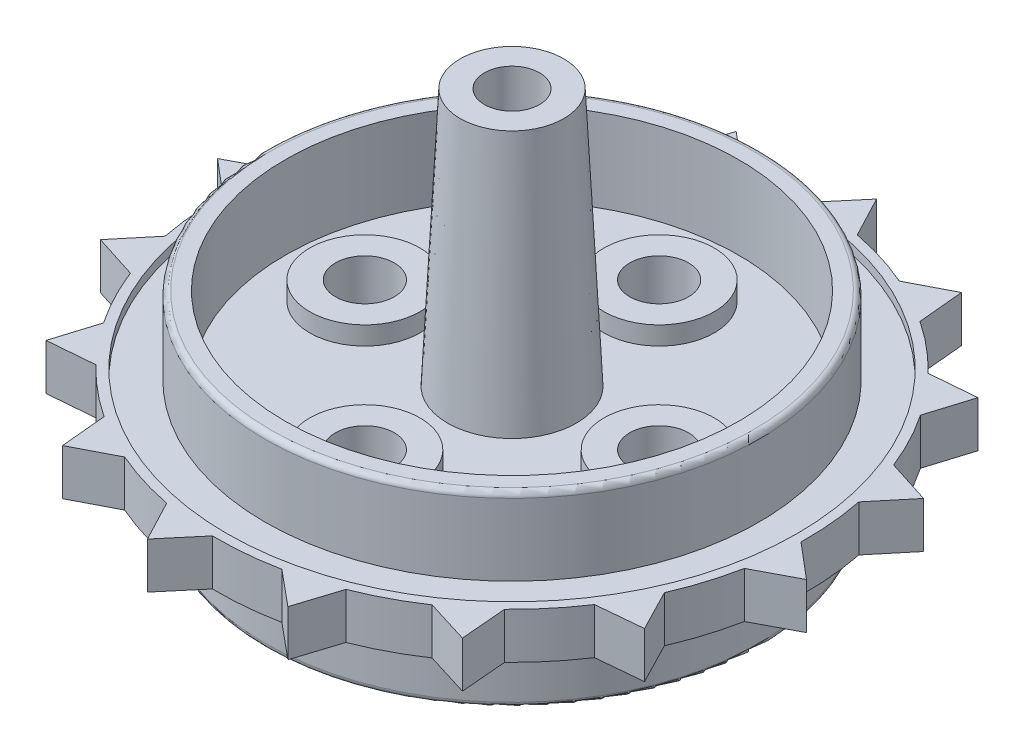
SolidWorks part; units mm, degrees
ref_plane "Front Plane" through (0, 0, 0) normal (0, 0, 1) x (1, 0, 0)
ref_plane "Top Plane" through (0, 0, 0) normal (0, 1, 0) x (1, 0, 0)
ref_plane "Right Plane" through (0, 0, 0) normal (1, 0, 0) x (0, 0, -1)
sketch "Sketch1" plane through (0, 0, 0) normal (0, 1, 0) x (1, 0, 0)
  circle A0 centre (0, 0) radius 13.425
  dimension "D1" = 26.85
extrude "Boss-Extrude1" add sketch "Sketch1" along normal blind 4
sketch "Sketch2" plane through (0, 4, 0) normal (0, 1, 0) x (1, 0, 0)
  circle A0 centre (0, 0) radius 16
  dimension "D1" = 32
extrude "Boss-Extrude2" add sketch "Sketch2" along normal blind 2.5
sketch "Sketch4" plane through (0, 0, 0) normal (0, -1, 0) x (1, 0, 0)
  circle A0 centre (0, 0) radius 12.325
  circle A1 centre (0, 0) radius 13.425 construction
  dimension "D1" = 1.1
extrude "Cut-Extrude1" cut sketch "Sketch4" against normal blind 4
sketch "Sketch5" plane through (0, 4, 0) normal (0, -1, 0) x (1, 0, 0)
  circle A0 centre (0, 0) radius 15.5
  circle A1 centre (0, 0) radius 16 construction
  dimension "D1" = 0.5
sketch "Sketch6" plane through (0, 6.5, 0) normal (0, 1, 0) x (1, 0, 0)
  circle A0 centre (0, 0) radius 15.5
  circle A1 centre (0, 0) radius 16 construction
  dimension "D1" = 0.5
extrude "Cut-Extrude3" cut sketch "Sketch6" against normal blind 0.5
extrude "Cut-Extrude4" cut sketch "Sketch5" against normal blind 0.5
sketch "Sketch7" plane through (0, 4.5, 0) normal (0, -1, 0) x (1, 0, 0)
  circle A0 centre (0, 0) radius 5.5
  circle A1 centre (0, 8) radius 3
  circle A2 centre (8, 0) radius 3
  circle A3 centre (0, -8) radius 3
  circle A4 centre (-8, 0) radius 3
  point P14 (0, 0)
  dimension "D1" = 11
  dimension "D2" = 6
  dimension "D3" = 8
  dimension "D4" = 0
  dimension "D6" = 11.3137
  dimension "D5" = 4
extrude "Boss-Extrude4" add sketch "Sketch7" along normal blind 1 contours A0 | A1 | A4 | A3 | A2
sketch "Sketch8" plane through (0, 3.5, 0) normal (0, -1, 0) x (1, 0, 0)
  circle A0 centre (0, 0) radius 3.2
  dimension "D1" = 6.4
extrude "Boss-Extrude5" add sketch "Sketch8" along normal blind 4.3
fillet "Fillet1" radius 1 1 edges at (0, -0.8, -3.2)
sketch "Sketch10" plane through (0, 6, 0) normal (0, 1, 0) x (1, 0, 0)
  circle A0 centre (0, 0) radius 13.425
  dimension "D1" = 26.85
extrude "Boss-Extrude6" add sketch "Sketch10" along normal blind 4.2
sketch "Sketch11" plane through (0, 10.2, 0) normal (0, 1, 0) x (1, 0, 0)
  circle A0 centre (0, 0) radius 12.325
  circle A1 centre (0, 0) radius 13.425 construction
  dimension "D1" = 1.1
extrude "Cut-Extrude6" cut sketch "Sketch11" against normal blind 4.5
sketch "Sketch12" plane through (0, 5.7, 0) normal (0, 1, 0) x (1, 0, 0)
  circle A0 centre (0, 0) radius 3.5
  dimension "D1" = 7
extrude "Boss-Extrude7" add sketch "Sketch12" along normal blind 14 draft 2.8
sketch "Sketch13" plane through (0, 19.7, 0) normal (0, 1, 0) x (1, 0, 0)
  circle A0 centre (0, 0) radius 1.5
  dimension "D1" = 3
extrude "Cut-Extrude7" cut sketch "Sketch13" against normal blind 14
fillet "Fillet2" radius 0.3 1 edges at (0, 0, 13.425)
fillet "Fillet3" radius 0.3 1 edges at (0, 10.2, 13.425)
sketch "Sketch14" plane through (0, 3.5, 0) normal (0, -1, 0) x (1, 0, 0)
  circle A0 centre (0, -8) radius 1.6
  arc A1 (-1.3642, -5.3281) -> (1.3642, -5.3281) centre (0, -8) ccw construction
  circle A2 centre (-8, 0) radius 1.6
  circle A3 centre (0, 8) radius 1.6
  circle A4 centre (8, 0) radius 1.6
  point P14 (0, 0)
  dimension "D1" = 3.2
  dimension "D2" = 0
  dimension "D3" = 4
extrude "Cut-Extrude8" cut sketch "Sketch14" against normal blind 5
sketch "Sketch15" plane through (0, 5.7, 0) normal (0, 1, 0) x (1, 0, 0)
  circle A0 centre (8, 0) radius 3
  circle A1 centre (0, -8) radius 3
  circle A2 centre (-8, 0) radius 3
  circle A3 centre (0, 8) radius 3
  circle A4 centre (8, 0) radius 1.6
  circle A5 centre (0, -8) radius 1.6
  circle A6 centre (-8, 0) radius 1.6
  circle A7 centre (0, 8) radius 1.6
  point P12 (0, 0)
  point P20 (0, 0)
  dimension "D1" = 6
  dimension "D2" = 4
  dimension "D3" = 4
extrude "Boss-Extrude8" add sketch "Sketch15" along normal blind 1
sketch "Sketch16" plane through (0, 4, 0) normal (0, -1, 0) x (1, 0, 0)
  line L0 (-11.1094, -11.5144) -> (-11.32, -14.0144)
  line L1 (-11.32, -14.0144) -> (-8.932, -13.2748)
  line L2 (-8.932, -13.2748) -> (-11.1094, -11.5144)
  line L3 (-14.6701, -6.3866) -> (-15.8214, -8.6156)
  line L4 (-15.8214, -8.6156) -> (-13.3321, -8.8462)
  line L5 (-13.3321, -8.8462) -> (-14.6701, -6.3866)
  line L6 (-15.9974, -0.2864) -> (-17.9142, -1.9052)
  line L7 (-17.9142, -1.9052) -> (-15.7025, -3.0708)
  line L8 (-15.7025, -3.0708) -> (-15.9974, -0.2864)
  line L9 (-14.8893, 5.8573) -> (-17.2796, 5.0953)
  line L10 (-17.2796, 5.0953) -> (-15.6824, 3.172)
  line L11 (-15.6824, 3.172) -> (-14.8893, 5.8573)
  line L12 (-11.5144, 11.1094) -> (-14.0144, 11.32)
  line L13 (-14.0144, 11.32) -> (-13.2748, 8.932)
  line L14 (-13.2748, 8.932) -> (-11.5144, 11.1094)
  line L15 (-6.3866, 14.6701) -> (-8.6156, 15.8214)
  line L16 (-8.6156, 15.8214) -> (-8.8462, 13.3321)
  line L17 (-8.8462, 13.3321) -> (-6.3866, 14.6701)
  line L18 (-0.2864, 15.9974) -> (-1.9052, 17.9142)
  line L19 (-1.9052, 17.9142) -> (-3.0708, 15.7025)
  line L20 (-3.0708, 15.7025) -> (-0.2864, 15.9974)
  line L21 (5.8573, 14.8893) -> (5.0953, 17.2796)
  line L22 (5.0953, 17.2796) -> (3.172, 15.6824)
  line L23 (3.172, 15.6824) -> (5.8573, 14.8893)
  line L24 (11.1094, 11.5144) -> (11.32, 14.0144)
  line L25 (11.32, 14.0144) -> (8.932, 13.2748)
  line L26 (8.932, 13.2748) -> (11.1094, 11.5144)
  line L27 (14.6701, 6.3866) -> (15.8214, 8.6156)
  line L28 (15.8214, 8.6156) -> (13.3321, 8.8462)
  line L29 (13.3321, 8.8462) -> (14.6701, 6.3866)
  line L30 (15.9974, 0.2864) -> (17.9142, 1.9052)
  line L31 (17.9142, 1.9052) -> (15.7025, 3.0708)
  line L32 (15.7025, 3.0708) -> (15.9974, 0.2864)
  line L33 (14.8893, -5.8573) -> (17.2796, -5.0953)
  line L34 (17.2796, -5.0953) -> (15.6824, -3.172)
  line L35 (15.6824, -3.172) -> (14.8893, -5.8573)
  line L36 (11.5144, -11.1094) -> (14.0144, -11.32)
  line L37 (14.0144, -11.32) -> (13.2748, -8.932)
  line L38 (13.2748, -8.932) -> (11.5144, -11.1094)
  line L39 (6.3866, -14.6701) -> (8.6156, -15.8214)
  line L40 (8.6156, -15.8214) -> (8.8462, -13.3321)
  line L41 (8.8462, -13.3321) -> (6.3866, -14.6701)
  line L42 (0.2864, -15.9974) -> (1.9052, -17.9142)
  line L43 (1.9052, -17.9142) -> (3.0708, -15.7025)
  line L44 (3.0708, -15.7025) -> (0.2864, -15.9974)
  line L45 (-5.8573, -14.8893) -> (-5.0953, -17.2796)
  line L46 (-5.0953, -17.2796) -> (-3.172, -15.6824)
  line L47 (-3.172, -15.6824) -> (-5.8573, -14.8893)
  circle A0 centre (0, 0) radius 16 construction
  point P53 (0, 0)
  dimension "D1" = 2.8
  dimension "D2" = 2.5
  dimension "D3" = 2.5
  dimension "D4" = 16
extrude "Boss-Extrude9" add sketch "Sketch16" against normal up to surface (2.5 mm away) up to face at (0, 6.5, 15.5)
